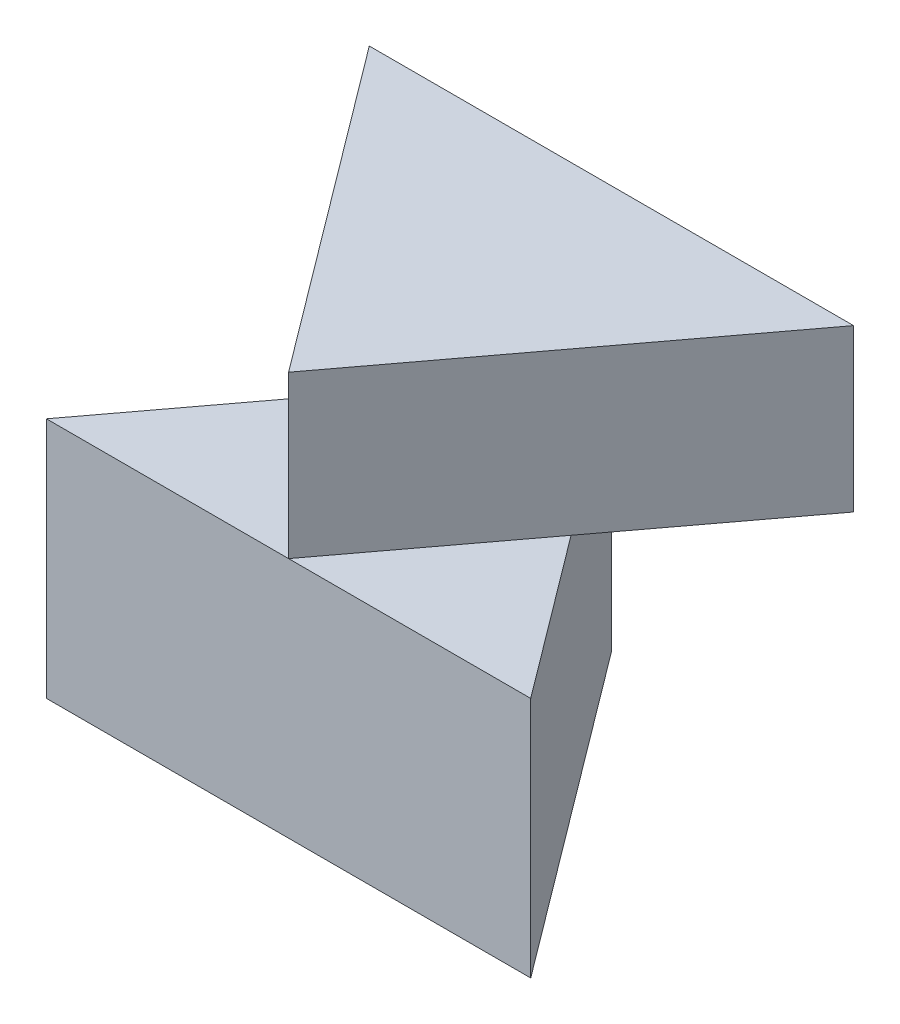
SolidWorks part; units mm, degrees
ref_plane "Front Plane" through (0, 0, 0) normal (0, 0, 1) x (1, 0, 0)
ref_plane "Top Plane" through (0, 0, 0) normal (0, 1, 0) x (1, 0, 0)
ref_plane "Right Plane" through (0, 0, 0) normal (1, 0, 0) x (0, 0, -1)
sketch "Sketch1" plane through (0, 0, 0) normal (0, 1, 0) x (1, 0, 0)
  line L3 (0, 4) -> (-3, 0)
  line L4 (-3, 0) -> (3, 0)
  line L5 (3, 0) -> (0, 4)
extrude "Boss-Extrude1" add sketch "Sketch1" along normal blind 3
sketch "Sketch2" plane through (0, 3, 0) normal (0, 1, 0) x (1, 0, 0)
  line L0 (0, 0) -> (-3, 4)
  line L2 (-3, 0) -> (3, 0) construction
  line L3 (-3, 4) -> (3, 4)
  line L4 (3, 4) -> (0, 0)
  dimension "D1" = 6
  dimension "D2" = 3
  dimension "D3" = 4
extrude "Boss-Extrude2" add sketch "Sketch2" along normal blind 2
